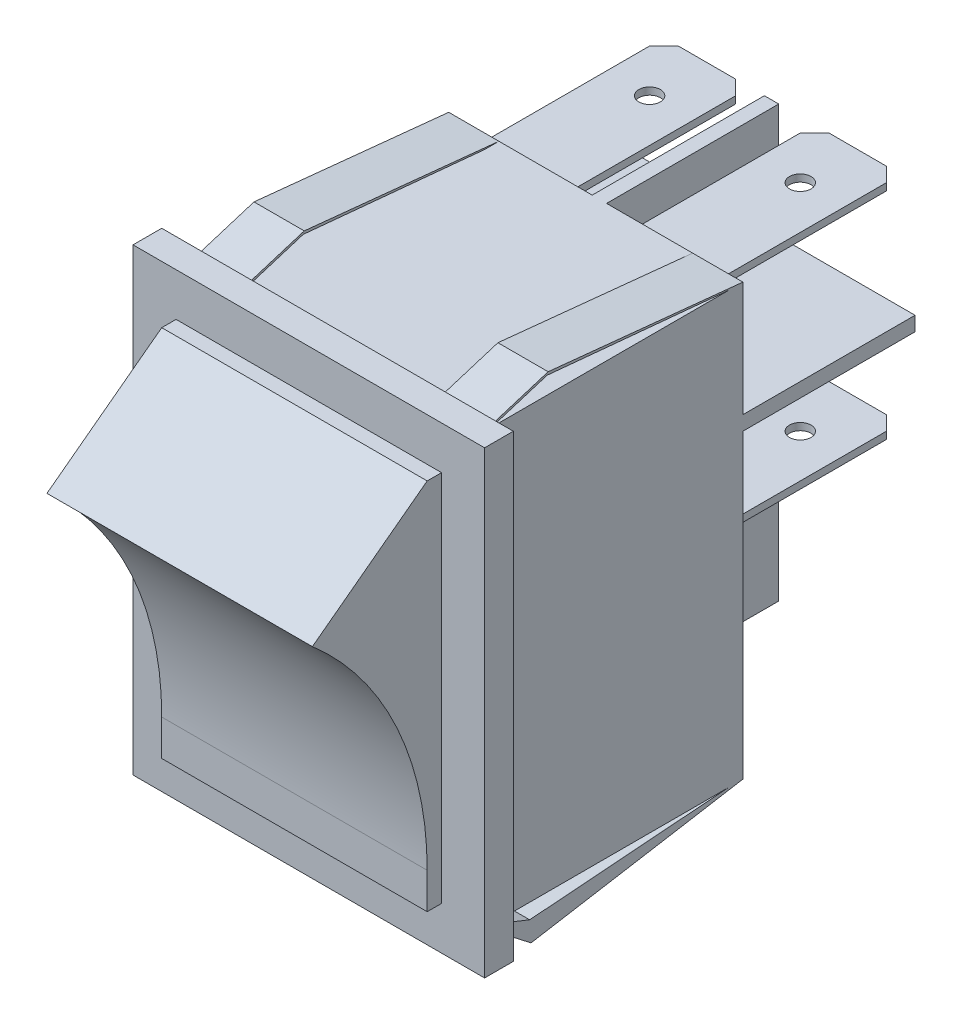
SolidWorks part; units mm, degrees
ref_plane "Front Plane" through (0, 0, 0) normal (0, 0, 1) x (1, 0, 0)
ref_plane "Top Plane" through (0, 0, 0) normal (0, 1, 0) x (1, 0, 0)
ref_plane "Right Plane" through (0, 0, 0) normal (1, 0, 0) x (0, 0, -1)
sketch "Sketch1" plane through (0, 0, 0) normal (0, 0, 1) x (1, 0, 0)
  line L1 (-13.9164, 23.4334) -> (10.5836, 23.4334)
  line L2 (-13.9164, 23.4334) -> (-13.9164, -8.5666)
  line L3 (-13.9164, -8.5666) -> (10.5836, -8.5666)
  line L4 (10.5836, 23.4334) -> (10.5836, -8.5666)
  dimension "D1" = 24.5
  dimension "D2" = 32
extrude "Extrude2" add sketch "Sketch1" along normal blind 2
sketch "Sketch2" plane through (0, 0, 0) normal (0, 0, -1) x (-1, 0, 0)
  line L0 (-10.5836, 23.4334) -> (13.9164, 23.4334) construction
  line L1 (-8.5836, 22.4334) -> (11.9164, 22.4334)
  line L2 (-8.5836, 22.4334) -> (-8.5836, -7.5666)
  line L3 (-8.5836, -7.5666) -> (11.9164, -7.5666)
  line L4 (11.9164, 22.4334) -> (11.9164, -7.5666)
  line L5 (-10.5836, -8.5666) -> (-10.5836, 23.4334) construction
  line L6 (13.9164, 23.4334) -> (13.9164, -8.5666) construction
  line L7 (13.9164, -8.5666) -> (-10.5836, -8.5666) construction
  dimension "D1" = 1
  dimension "D2" = 2
  dimension "D3" = 2
  dimension "D4" = 1
extrude "Extrude3" add sketch "Sketch2" along normal blind 18
sketch "Sketch4" plane through (0, 0, 2) normal (0, 0, 1) x (1, 0, 0)
  line L0 (10.5836, 23.4334) -> (-13.9164, 23.4334) construction
  line L1 (-10.9164, 20.4334) -> (7.5836, 20.4334)
  line L2 (-10.9164, 20.4334) -> (-10.9164, -5.5666)
  line L3 (-10.9164, -5.5666) -> (7.5836, -5.5666)
  line L4 (7.5836, -5.5666) -> (7.5836, 20.4334)
  line L5 (-13.9164, 23.4334) -> (-13.9164, -8.5666) construction
  line L6 (10.5836, -8.5666) -> (10.5836, 23.4334) construction
  line L7 (-13.9164, -8.5666) -> (10.5836, -8.5666) construction
  dimension "D1" = 3
  dimension "D2" = 3
  dimension "D3" = 3
  dimension "D4" = 3
extrude "Extrude7" add sketch "Sketch4" along normal blind 1
sketch "Sketch5" plane through (-10.9164, 0, 0) normal (-1, 0, 0) x (0, 0, 1)
  line L0 (3, 20.4334) -> (3, -3.0657)
  line L1 (3, 20.4334) -> (3, -5.5666) construction
  line L2 (3, 20.4334) -> (11, 14.4334)
  arc A0 (3, -3.0657) -> (11, 14.4334) centre (26.1387, -3.0657) cw
  dimension "D1" = 8
  dimension "D2" = 10
extrude "Extrude8" add sketch "Sketch5" against normal blind 18.5
sketch "Sketch6" plane through (-11.9164, 0, 0) normal (-1, 0, 0) x (0, 0, 1)
  line L0 (-18, 22.4334) -> (-17, 22.4334)
  line L1 (-18, 22.4334) -> (0, 22.4334) construction
  line L2 (-17, 22.4334) -> (-4.3597, 23.6325)
  line L3 (-4.3597, 23.6325) -> (-0.5, 22.4334)
  line L4 (-0.5, 22.4334) -> (0, 22.4334)
  line L5 (0, 22.4334) -> (-4.43, 23.8097)
  line L6 (-4.43, 23.8097) -> (-18, 22.4334)
  dimension "D1" = 0.5
  dimension "D2" = 1
extrude "Extrude9" add sketch "Sketch6" against normal blind 3.5
sketch "Sketch7" plane through (8.5836, 0, 0) normal (1, 0, 0) x (0, 0, -1)
  line L0 (18, 22.4334) -> (17.0017, 22.4334)
  line L1 (18, 22.4334) -> (0, 22.4334) construction
  line L2 (17.0017, 22.4334) -> (4.3597, 23.6325)
  line L3 (4.3597, 23.6325) -> (0.5, 22.4334)
  line L4 (0.5, 22.4334) -> (0, 22.4334)
  line L5 (0, -8.5666) -> (0, 23.4334) construction
  line L6 (0.5, 22.4334) -> (0, 22.4334) construction
  line L7 (0, 22.4334) -> (4.43, 23.8097)
  line L8 (4.43, 23.8097) -> (18, 22.4334)
extrude "Extrude10" add sketch "Sketch7" against normal blind 3.5
sketch "Sketch8" plane through (8.5836, 0, 0) normal (1, 0, 0) x (0, 0, -1)
  line L0 (0, -7.5666) -> (0.5, -7.5666)
  line L1 (18, -7.5666) -> (0, -7.5666) construction
  line L2 (0.5, -7.5666) -> (3.1411, -8.6239)
  line L3 (3.1411, -8.6239) -> (17, -7.5666)
  line L4 (17, -7.5666) -> (18, -7.5666)
  line L5 (18, -7.5666) -> (3.2375, -10.0666)
  line L6 (3.2375, -10.0666) -> (0, -7.5666)
  dimension "D1" = 0.5
  dimension "D2" = 1
  dimension "D3" = 2.5
extrude "Extrude11" add sketch "Sketch8" against normal blind 3.5
sketch "Sketch9" plane through (-11.9164, 0, 0) normal (-1, 0, 0) x (0, 0, 1)
  line L0 (0, -7.5666) -> (-0.5601, -7.5666)
  line L1 (-18, -7.5666) -> (0, -7.5666) construction
  line L2 (-0.5601, -7.5666) -> (-3.1411, -8.6239)
  line L3 (-3.1411, -8.6239) -> (-17, -7.5666)
  line L4 (-17, -7.5666) -> (-18, -7.5666)
  line L5 (-18, -7.5666) -> (-3.2375, -10.0666)
  line L6 (-3.2375, -10.0666) -> (0, -7.5666)
extrude "Extrude12" add sketch "Sketch9" against normal blind 3.5
sketch "Sketch10" plane through (0, 0, -18) normal (0, 0, -1) x (-1, 0, 0)
  line L0 (8.4164, 22.4334) -> (-5.0836, 22.4334) construction
  line L1 (0.9164, 22.4334) -> (1.9164, 22.4334)
  line L2 (0.9164, 22.4334) -> (0.9164, -7.5666)
  line L3 (0.9164, -7.5666) -> (1.9164, -7.5666)
  line L4 (1.9164, 22.4334) -> (1.9164, -7.5666)
  line L5 (-5.0836, -7.5666) -> (8.4164, -7.5666) construction
  line L6 (-8.5836, 22.4334) -> (-8.5836, -7.5666) construction
  dimension "D1" = 1
  dimension "D2" = 9.5
extrude "Extrude13" add sketch "Sketch10" along normal blind 12
sketch "Sketch11" plane through (0, 0, -18) normal (0, 0, -1) x (-1, 0, 0)
  line L0 (0.9164, 22.4334) -> (0.9164, -7.5666) construction
  line L1 (0.9164, 13.4334) -> (-8.5836, 13.4334)
  line L2 (0.9164, 13.4334) -> (0.9164, 14.4334)
  line L3 (0.9164, 14.4334) -> (-8.5836, 14.4334)
  line L4 (-8.5836, 13.4334) -> (-8.5836, 14.4334)
  line L5 (-8.5836, 22.4334) -> (-8.5836, -7.5666) construction
  line L6 (-5.0836, 22.4334) -> (-8.5836, 22.4334) construction
  line L7 (1.9164, -7.5666) -> (1.9164, 22.4334) construction
  line L8 (1.9164, 14.4334) -> (11.9164, 14.4334)
  line L9 (1.9164, 14.4334) -> (1.9164, 13.4334)
  line L10 (1.9164, 13.4334) -> (11.9164, 13.4334)
  line L11 (11.9164, 14.4334) -> (11.9164, 13.4334)
  line L12 (11.9164, -7.5666) -> (11.9164, 22.4334) construction
  dimension "D1" = 1
  dimension "D2" = 8
extrude "Extrude14" add sketch "Sketch11" along normal blind 12
sketch "Sketch12" plane through (0, 0, -18) normal (0, 0, -1) x (-1, 0, 0)
  line L0 (11.9164, 14.4334) -> (11.9164, 22.4334) construction
  line L1 (-6.5836, 21.4334) -> (-0.5836, 21.4334)
  line L2 (-6.5836, 21.4334) -> (-6.5836, 20.9334)
  line L3 (-6.5836, 20.9334) -> (-0.5836, 20.9334)
  line L4 (-0.5836, 21.4334) -> (-0.5836, 20.9334)
  line L5 (3.9164, 21.4334) -> (9.9164, 21.4334)
  line L6 (3.9164, 21.4334) -> (3.9164, 20.9334)
  line L7 (3.9164, 20.9334) -> (9.9164, 20.9334)
  line L8 (9.9164, 21.4334) -> (9.9164, 20.9334)
  line L9 (-6.5836, 6.4334) -> (-0.5836, 6.4334)
  line L10 (-6.5836, 6.4334) -> (-6.5836, 5.9334)
  line L11 (-6.5836, 5.9334) -> (-0.5836, 5.9334)
  line L12 (-0.5836, 6.4334) -> (-0.5836, 5.9334)
  line L13 (3.9164, 6.4334) -> (9.9164, 6.4334)
  line L14 (3.9164, 6.4334) -> (3.9164, 5.9334)
  line L15 (3.9164, 5.9334) -> (9.9164, 5.9334)
  line L16 (9.9164, 6.4334) -> (9.9164, 5.9334)
  line L25 (11.9164, -7.5666) -> (11.9164, 13.4334) construction
  line L27 (-8.5836, 22.4334) -> (-8.5836, 14.4334) construction
  line L28 (-8.5836, 22.4334) -> (-8.5836, -7.5666) construction
  line L29 (-8.5836, 13.4334) -> (0.9164, 13.4334) construction
  line L30 (1.9164, 13.4334) -> (11.9164, 13.4334) construction
  line L31 (8.4164, 22.4334) -> (-5.0836, 22.4334) construction
  dimension "D1" = 6
  dimension "D2" = 6
  dimension "D3" = 6
  dimension "D4" = 6
  dimension "D7" = 2
  dimension "D8" = 2
  dimension "D10" = 2
  dimension "D11" = 2
  dimension "D13" = 0.5
  dimension "D14" = 0.5
  dimension "D16" = 0.5
  dimension "D17" = 0.5
  dimension "D19" = 7
  dimension "D20" = 7
  dimension "D21" = 1
  dimension "D24" = 1
extrude "Extrude15" add sketch "Sketch12" along normal blind 13
chamfer "Chamfer1" distance 1 angle 45 8 edges at (-9.9164, 6.1834, -31) (-3.9164, 6.1834, -31) (0.5836, 6.1834, -31) (6.5836, 6.1834, -31) (-9.9164, 21.1834, -31) (-3.9164, 21.1834, -31) (0.5836, 21.1834, -31) (6.5836, 21.1834, -31)
sketch "Sketch13" plane through (0, 6.4334, 0) normal (0, -1, 0) x (1, 0, 0)
  line L4 (6.5836, -30) -> (6.5836, -18) construction
  line L6 (5.5836, -31) -> (1.5836, -31) construction
  line L7 (-4.9164, -31) -> (-8.9164, -31) construction
  line L8 (-9.9164, -30) -> (-9.9164, -18) construction
  circle A0 centre (-6.9164, -27) radius 0.75
  circle A1 centre (3.5836, -27) radius 0.75
  dimension "D1" = 1.5
  dimension "D2" = 1.5
  dimension "D3" = 3
  dimension "D4" = 4
  dimension "D5" = 4
  dimension "D6" = 3
sketch "Sketch14" plane through (0, 21.4334, 0) normal (0, 1, 0) x (1, 0, 0)
  line L0 (0.5836, 30) -> (0.5836, 18) construction
  line L1 (-9.9164, 30) -> (-9.9164, 18) construction
  line L2 (-8.9164, 31) -> (-4.9164, 31) construction
  line L3 (1.5836, 31) -> (5.5836, 31) construction
  circle A0 centre (-6.9164, 27) radius 0.75
  circle A1 centre (3.5836, 27) radius 0.75
  dimension "D1" = 1.5
  dimension "D2" = 1.5
  dimension "D3" = 3
  dimension "D4" = 3
  dimension "D5" = 4
  dimension "D6" = 4
extrude "Cut-Extrude2" cut sketch "Sketch14" against normal blind 1
extrude "Taglio-Estrusione1" cut sketch "Sketch13" along normal up to next
